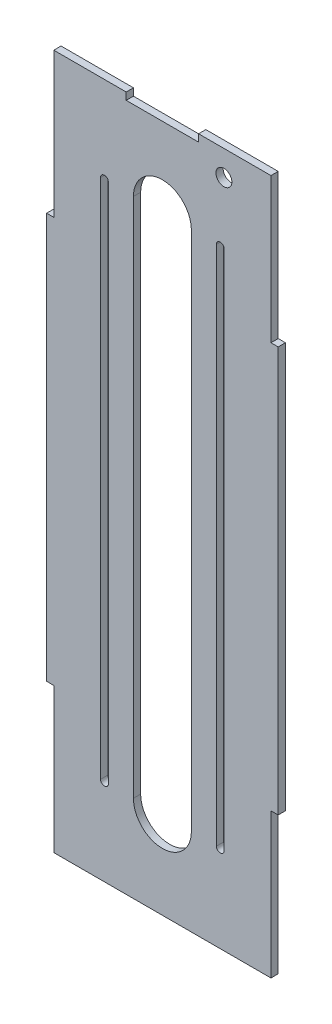
SolidWorks part; units mm, degrees
ref_plane "Front Plane" through (0, 0, 0) normal (0, 0, 1) x (1, 0, 0)
ref_plane "Top Plane" through (0, 0, 0) normal (0, 1, 0) x (1, 0, 0)
ref_plane "Right Plane" through (0, 0, 0) normal (1, 0, 0) x (0, 0, -1)
sketch "Sketch2" plane through (0, 0, 0) normal (0, 0, 1) x (1, 0, 0)
  line L1 (-803.1768, 65.3086) -> (-1019.0768, 65.3086)
  line L2 (-803.1768, 65.3086) -> (-803.1768, 674.9086)
  line L3 (-803.1768, 674.9086) -> (-1019.0768, 674.9086)
  line L4 (-1019.0768, 65.3086) -> (-1019.0768, 674.9086)
  line L5 (-803.1768, 65.3086) -> (-1019.0768, 674.9086) construction
  line L6 (-803.1768, 674.9086) -> (-1019.0768, 65.3086) construction
  dimension "D1" = 215.9
  dimension "D2" = 609.6
extrude "Boss-Extrude1" add sketch "Sketch2" along normal blind 6.35
sketch "Sketch3" plane through (0, 0, 6.35) normal (0, 0, 1) x (1, 0, 0)
  line L0 (-911.1268, 674.9086) -> (-911.1268, 65.3086) construction
  line L1 (-803.1768, 674.9086) -> (-1019.0768, 674.9086) construction
  line L2 (-1019.0768, 65.3086) -> (-803.1768, 65.3086) construction
  line L3 (-803.1768, 370.1086) -> (-1019.0768, 370.1086) construction
  line L4 (-803.1768, 65.3086) -> (-803.1768, 674.9086) construction
  line L5 (-1019.0768, 674.9086) -> (-1019.0768, 65.3086) construction
  line L6 (-911.1268, 141.5086) -> (-911.1268, 598.7086) construction
  line L7 (-936.5268, 141.5086) -> (-936.5268, 598.7086)
  line L8 (-885.7268, 141.5086) -> (-885.7268, 598.7086)
  arc A0 (-936.5268, 141.5086) -> (-885.7268, 141.5086) centre (-911.1268, 141.5086) ccw
  arc A1 (-885.7268, 598.7086) -> (-936.5268, 598.7086) centre (-911.1268, 598.7086) ccw
  point P14 (-911.1268, 370.1086)
extrude "Cut-Extrude1" cut sketch "Sketch3" against normal through all contours L8 A1 L7 A0
sketch "Sketch4" plane through (0, 0, 6.35) normal (0, 0, 1) x (1, 0, 0)
  line L0 (-815.8768, 674.9086) -> (-815.8768, 547.9086)
  line L1 (-803.1768, 674.9086) -> (-1019.0768, 674.9086) construction
  line L2 (-815.8768, 547.9086) -> (-803.1768, 547.9086)
  line L3 (-803.1768, 65.3086) -> (-803.1768, 674.9086) construction
extrude "Cut-Extrude2" cut sketch "Sketch4" against normal through all and the other way through all
sketch "Sketch5" plane through (0, 0, 6.35) normal (0, 0, 1) x (1, 0, 0)
  line L0 (-815.8768, 65.3086) -> (-815.8768, 192.3086)
  line L1 (-1019.0768, 65.3086) -> (-803.1768, 65.3086) construction
  line L2 (-815.8768, 192.3086) -> (-803.1768, 192.3086)
  line L3 (-803.1768, 65.3086) -> (-803.1768, 547.9086) construction
extrude "Cut-Extrude3" cut sketch "Sketch5" against normal through all and the other way through all flip side to cut
sketch "Sketch6" plane through (0, 0, 6.35) normal (0, 0, 1) x (1, 0, 0)
  line L0 (-1006.3768, 674.9086) -> (-1006.3768, 547.9086)
  line L1 (-815.8768, 674.9086) -> (-1019.0768, 674.9086) construction
  line L2 (-1006.3768, 547.9086) -> (-1019.0768, 547.9086)
  line L3 (-1019.0768, 674.9086) -> (-1019.0768, 65.3086) construction
extrude "Cut-Extrude6" cut sketch "Sketch6" against normal through all and the other way through all flip side to cut
ref_plane "Plane1" through (-1006.3768, 674.9086, 6.35) normal (-1, 0, 0) x (0, 0, 1)
sketch "Sketch9" plane through (0, 0, 6.35) normal (0, 0, 1) x (1, 0, 0)
  line L0 (-1006.3768, 65.3086) -> (-1006.3768, 192.3086)
  line L1 (-1019.0768, 65.3086) -> (-815.8768, 65.3086) construction
  line L2 (-1006.3768, 192.3086) -> (-1019.0768, 192.3086)
  line L3 (-1019.0768, 547.9086) -> (-1019.0768, 65.3086) construction
extrude "Cut-Extrude7" cut sketch "Sketch9" against normal through all and the other way through all
ref_plane "Plane2" through (-1006.3768, 65.3086, 6.35) normal (1, 0, 0) x (0, 0, -1)
sketch "Sketch13" plane through (0, 0, 0) normal (0, 0, -1) x (-1, 0, 0)
  line L2 (815.8768, 674.9086) -> (1006.3768, 674.9086) construction
  line L5 (879.3768, 668.5586) -> (879.3768, 674.9086)
  line L6 (942.8768, 668.5586) -> (942.8768, 674.9086)
  line L7 (942.8768, 668.5586) -> (879.3768, 668.5586)
ref_plane "Plane3" through (-803.1768, 192.3086, 0) normal (-1, 0, 0) x (0, 0, 1)
ref_plane "Plane10" through (-1019.0768, 192.3086, 6.35) normal (1, 0, 0) x (0, 0, -1)
sketch "Sketch16" plane through (0, 0, 6.35) normal (0, 0, 1) x (1, 0, 0)
  line L2 (-1012.7268, 192.3086) -> (-1012.7268, 547.9086)
  line L3 (-1019.0768, 192.3086) -> (-1006.3768, 192.3086) construction
  line L4 (-1019.0768, 547.9086) -> (-1006.3768, 547.9086) construction
extrude "Cut-Extrude11" cut sketch "Sketch16" against normal through all and the other way through all
sketch "Sketch17" plane through (0, 0, 6.35) normal (0, 0, 1) x (1, 0, 0)
  line L2 (-809.5268, 192.3086) -> (-809.5268, 547.9086)
  line L3 (-803.1768, 547.9086) -> (-815.8768, 547.9086) construction
extrude "Cut-Extrude13" cut sketch "Sketch17" against normal through all and the other way through all flip side to cut
extrude "Cut-Extrude14" cut sketch "Sketch13" against normal through all and the other way through all
ref_plane "Plane11" through (-936.5268, 141.5086, 0) normal (0, 1, 0) x (1, 0, 0)
sketch "Sketch25" plane through (0, 0, 0) normal (0, 0, -1) x (-1, 0, 0)
  line L1 (961.9268, 141.5086) -> (961.9268, 598.7086) construction
  line L3 (958.4978, 141.5086) -> (958.4978, 598.7086)
  line L6 (965.3558, 141.5086) -> (965.3558, 598.7086)
  line L7 (860.3268, 141.5086) -> (860.3268, 598.7086) construction
  line L8 (856.8978, 141.5086) -> (856.8978, 598.7086) construction
  line L9 (863.7558, 141.5086) -> (863.7558, 598.7086) construction
  arc A0 (958.4978, 141.5086) -> (965.3558, 141.5086) centre (961.9268, 141.5086) ccw
  arc A1 (965.3558, 598.7086) -> (958.4978, 598.7086) centre (961.9268, 598.7086) ccw
  arc A2 (856.8978, 141.5086) -> (863.7558, 141.5086) centre (860.3268, 141.5086) ccw construction
  arc A3 (863.7558, 598.7086) -> (856.8978, 598.7086) centre (860.3268, 598.7086) ccw construction
  point P10 (961.9268, 370.1086)
  point P17 (860.3268, 370.1086)
extrude "Cut-Extrude19" cut sketch "Sketch25" against normal through all contours L3 A1 L6 A0
ref_plane "Plane15" through (-911.1268, 0, 0) normal (1, 0, 0) x (0, 0, -1)
mirror "Mirror1" about plane through (-911.1268, 0, 0) normal (1, 0, 0) of "Cut-Extrude19"
sketch "Sketch26" plane through (0, 0, 6.35) normal (0, 0, 1) x (1, 0, 0)
  circle A0 centre (-857.1585, 652.7849) radius 6.985
extrude "Cut-Extrude20" cut sketch "Sketch26" against normal through all
